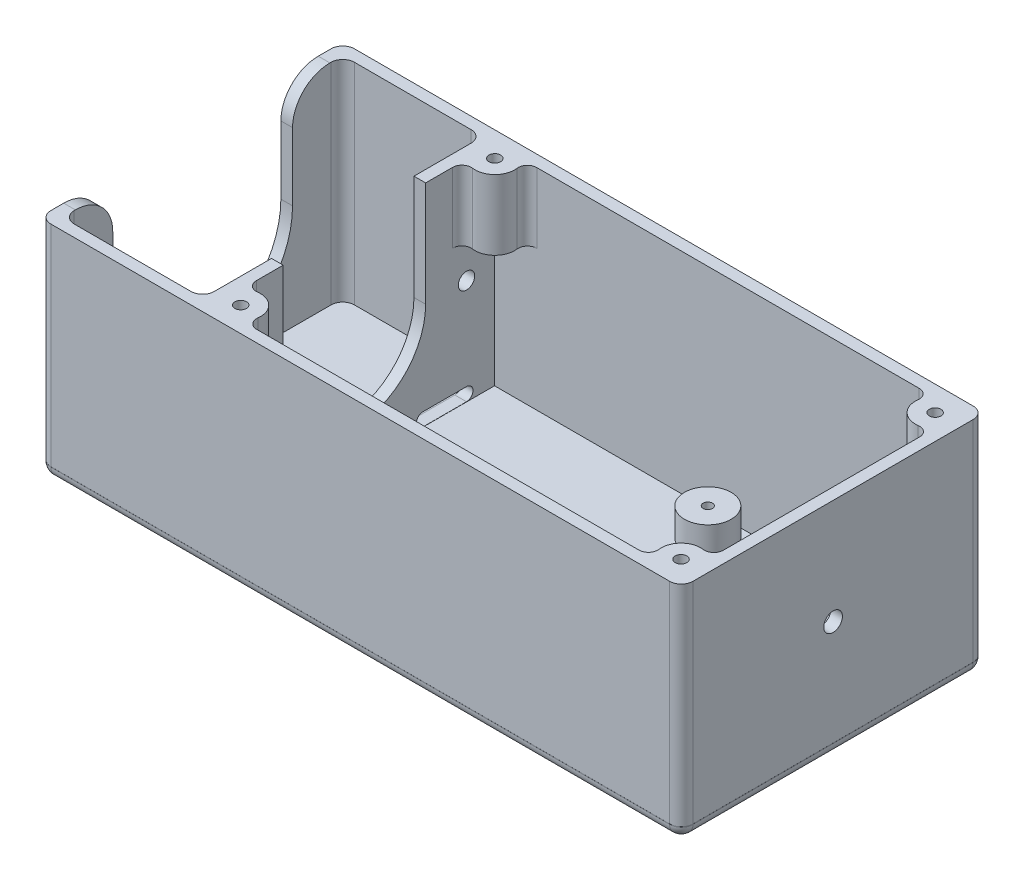
SolidWorks part; units mm, degrees
ref_plane "Спереди" through (0, 0, 0) normal (0, 0, 1) x (1, 0, 0)
ref_plane "Сверху" through (0, 0, 0) normal (0, 1, 0) x (1, 0, 0)
ref_plane "Справа" through (0, 0, 0) normal (1, 0, 0) x (0, 0, -1)
sketch "Эскиз1" plane through (0, 0, 0) normal (0, 1, 0) x (1, 0, 0)
  line L0 (-34.5539, 0) -> (36.3395, 0) construction
  line L1 (-40.9449, 30) -> (40.9449, 30)
  line L2 (-50, 21.0165) -> (-50, -21.0165)
  line L3 (-40.9449, -30) -> (40.9449, -30)
  line L4 (50, 21.0165) -> (50, -21.0165)
  line L5 (-82.5, 32.5) -> (50, 32.5)
  line L6 (-85, 30) -> (-85, -30)
  line L7 (-82.5, -32.5) -> (50, -32.5)
  line L8 (52.5, 30) -> (52.5, -30)
  line L9 (-80, 30) -> (-55, 30)
  line L10 (-82.5, 27.5) -> (-82.5, -27.5)
  line L11 (-80, -30) -> (-55, -30)
  line L12 (-52.5, 27.5) -> (-52.5, -27.5)
  arc A0 (50, 32.5) -> (52.5, 30) centre (50, 30) cw
  arc A1 (52.5, -30) -> (50, -32.5) centre (50, -30) cw
  arc A2 (-82.5, -32.5) -> (-85, -30) centre (-82.5, -30) cw
  arc A3 (-85, 30) -> (-82.5, 32.5) centre (-82.5, 30) cw
  arc A4 (-42.9287, 27.7464) -> (-40.9449, 30) centre (-40.9449, 28) cw
  arc A8 (-80, -30) -> (-82.5, -27.5) centre (-80, -27.5) cw
  arc A9 (-55, -30) -> (-52.5, -27.5) centre (-55, -27.5) ccw
  arc A10 (-52.5, 27.5) -> (-55, 30) centre (-55, 27.5) ccw
  arc A11 (-80, 30) -> (-82.5, 27.5) centre (-80, 27.5) ccw
  arc A12 (-47.7262, 22.9977) -> (-42.9287, 27.7464) centre (-47.1445, 27.2076) ccw
  circle A13 centre (-47.1445, 27.2076) radius 1.25
  arc A14 (-47.7262, 22.9977) -> (-50, 21.0165) centre (-48, 21.0165) ccw
  arc A15 (47.7262, -22.9977) -> (50, -21.0165) centre (48, -21.0165) ccw
  arc A16 (47.7262, -22.9977) -> (42.9287, -27.7464) centre (47.1445, -27.2076) ccw
  circle A17 centre (47.1445, -27.2076) radius 1.25
  arc A18 (42.9287, -27.7464) -> (40.9449, -30) centre (40.9449, -28) cw
  circle A19 centre (47.1445, 27.2076) radius 1.25
  arc A20 (47.7262, 22.9977) -> (50, 21.0165) centre (48, 21.0165) cw
  arc A21 (47.7262, 22.9977) -> (42.9287, 27.7464) centre (47.1445, 27.2076) cw
  arc A22 (42.9287, 27.7464) -> (40.9449, 30) centre (40.9449, 28) ccw
  arc A23 (-42.9287, -27.7464) -> (-40.9449, -30) centre (-40.9449, -28) ccw
  circle A24 centre (-47.1445, -27.2076) radius 1.25
  arc A25 (-47.7262, -22.9977) -> (-42.9287, -27.7464) centre (-47.1445, -27.2076) cw
  arc A26 (-47.7262, -22.9977) -> (-50, -21.0165) centre (-48, -21.0165) cw
  point P24 (-50, 30)
  point P27 (50, 30)
  point P32 (-50, -30)
  point P35 (-82.5, -30)
  point P38 (-52.5, -30)
  point P60 (0, 0)
  dimension "D11" = 2.5
  dimension "D12" = 2.5
  dimension "D13" = 3
  dimension "D14" = 2
  dimension "D15" = 2
  dimension "D1" = 100
  dimension "D3" = 2.5
  dimension "D4" = 2.5
  dimension "D5" = 2.5
  dimension "D6" = 2.5
  dimension "D7" = 2.5
  dimension "D8" = 2.5
  dimension "D9" = 30
  dimension "D10" = 2.5
  dimension "D16" = 50
  dimension "D17" = 30
  dimension "D18" = 2
extrude "Бобышка-Вытянуть1" add sketch "Эскиз1" along normal blind 45
sketch "Эскиз2" plane through (0, 0, 0) normal (0, -1, 0) x (1, 0, 0)
  line L1 (-82.499, -32.4879) -> (50.0112, -32.4879)
  line L2 (-84.999, -29.9879) -> (-84.999, 30.0121)
  line L3 (-82.499, 32.5121) -> (50.0112, 32.5121)
  line L4 (52.5112, -29.9879) -> (52.5112, 30.0121)
  arc A0 (50.0112, -32.4879) -> (52.5112, -29.9879) centre (50.0112, -29.9879) ccw
  arc A1 (52.5112, 30.0121) -> (50.0112, 32.5121) centre (50.0112, 30.0121) ccw
  arc A2 (-82.499, 32.5121) -> (-84.999, 30.0121) centre (-82.499, 30.0121) ccw
  arc A3 (-84.999, -29.9879) -> (-82.499, -32.4879) centre (-82.499, -29.9879) ccw
  dimension "D1" = 2.5
  dimension "D2" = 2.5
  dimension "D3" = 2.5
  dimension "D4" = 2.5
extrude "Бобышка-Вытянуть2" add sketch "Эскиз2" along normal blind 2.5
fillet "Скругление1" radius 2.4 8 edges at (-16.2439, -2.5, -32.4879) (-84.2668, -2.5, -31.7557) (-84.999, -2.5, 0.0121) (-84.2668, -2.5, 31.7798) (-16.2439, -2.5, 32.5121) (51.779, -2.5, 31.7798) (52.5112, -2.5, 0.0121) (51.779, -2.5, -31.7557)
sketch "Эскиз4" plane through (-52.5, 0, 0) normal (-1, 0, 0) x (0, 0, 1)
  line L0 (-15.25, 22.5) -> (-15.25, 45)
  line L1 (-15.25, 45) -> (15.25, 45)
  line L2 (15.25, 45) -> (15.25, 22.5)
  line L3 (14.672, 1.445) -> (24, 1.445) construction
  line L4 (14.672, 2.8458) -> (24, 2.8458)
  line L5 (14.672, 0.0443) -> (24, 0.0443)
  line L6 (0, 39.0115) -> (0, 10.7374) construction
  line L7 (-14.672, 1.445) -> (-24, 1.445) construction
  line L8 (-14.672, 2.8458) -> (-24, 2.8458)
  line L9 (-14.672, 0.0443) -> (-24, 0.0443)
  line L10 (-32.5, 45) -> (-32.5, 0) construction
  arc A0 (-15.25, 22.5) -> (15.25, 22.5) centre (0, 22.5) ccw
  circle A1 centre (-24, 22.5) radius 1.75
  circle A2 centre (24, 22.5) radius 1.75
  arc A3 (14.672, 2.8458) -> (14.672, 0.0443) centre (14.672, 1.445) ccw
  arc A4 (24, 0.0443) -> (24, 2.8458) centre (24, 1.445) ccw
  arc A5 (-14.672, 2.8458) -> (-14.672, 0.0443) centre (-14.672, 1.445) cw
  arc A6 (-24, 0.0443) -> (-24, 2.8458) centre (-24, 1.445) cw
  point P14 (19.336, 1.445)
  point P27 (-19.336, 1.445)
  dimension "D1" = 3.5
  dimension "D2" = 3.5
  dimension "D5" = 30.5
  dimension "D3" = 48
  dimension "D4" = 24
  dimension "D6" = 17.25
  dimension "D7" = 22.5
extrude "Вырез-Вытянуть1" cut sketch "Эскиз4" against normal up to next
sketch "Эскиз5" plane through (-50, 0, 0) normal (1, 0, 0) x (0, 0, -1)
  line L0 (-30, 45) -> (-30, 0) construction
  line L1 (-30, 30.0197) -> (30, 30.0197)
  line L2 (-30, 30.0197) -> (-30, 0)
  line L3 (-30, 0) -> (30, 0)
  line L4 (30, 30.0197) -> (30, 0)
extrude "Вырез-Вытянуть2" cut sketch "Эскиз5" along normal up to surface (100 mm away) up to face at (50, 22.5, 0)
sketch "Эскиз7" plane through (52.5, 0, 0) normal (1, 0, 0) x (0, 0, -1)
  line L0 (-30, 45) -> (30, 0) construction
  line L1 (30, 45) -> (-30.0121, -0.1) construction
  circle A0 centre (0, 22.5) radius 2
extrude "Вырез-Вытянуть3" cut sketch "Эскиз7" against normal blind 2.5
sketch "Эскиз8" plane through (0, 0, 0) normal (0, 1, 0) x (1, 0, 0)
  circle A0 centre (1.0914, 24.5834) radius 1
  circle A1 centre (1.0914, 24.5834) radius 5
  circle A2 centre (38.0914, 24.5834) radius 5
  circle A3 centre (38.0914, 24.5834) radius 1
  circle A4 centre (38.0914, -12.4166) radius 5
  circle A5 centre (38.0914, -12.4166) radius 1
  circle A6 centre (1.0914, -12.4166) radius 5
  circle A7 centre (1.0914, -12.4166) radius 1
  dimension "D5" = 2
  dimension "D8" = 4
  dimension "D9" = 4
extrude "Бобышка-Вытянуть7" add sketch "Эскиз8" along normal blind 6
sketch "Эскиз10" plane through (-85, 0, 0) normal (-1, 0, 0) x (0, 0, 1)
  line L0 (-19.25, 22.5) -> (-19.25, 37)
  line L2 (-27.25, 45) -> (27.25, 45)
  line L3 (19.25, 37) -> (19.25, 22.5)
  arc A0 (-19.25, 22.5) -> (19.25, 22.5) centre (0, 22.5) ccw
  arc A1 (-19.25, 37) -> (-27.25, 45) centre (-27.25, 37) ccw
  arc A2 (19.25, 37) -> (27.25, 45) centre (27.25, 37) cw
  dimension "D1" = 38.5
  dimension "D2" = 8
  dimension "D3" = 8
extrude "Вырез-Вытянуть4" cut sketch "Эскиз10" against normal up to next
